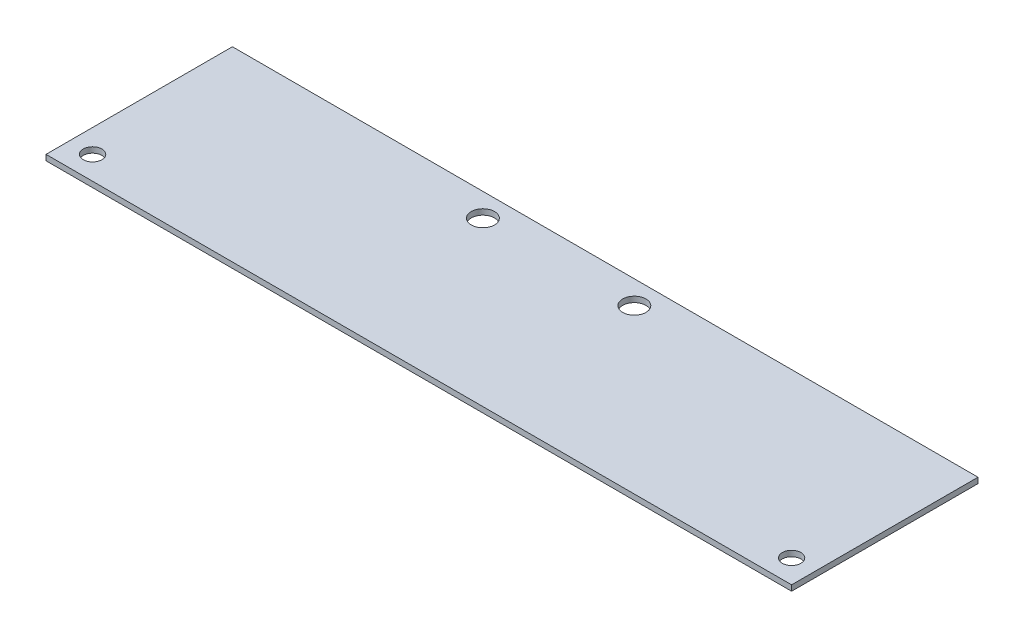
SolidWorks part; units mm, degrees
material "1023 Carbon Steel Sheet (SS)"
ref_plane "Front Plane" through (0, 0, 0) normal (0, 0, 1) x (1, 0, 0)
ref_plane "Top Plane" through (0, 0, 0) normal (0, 1, 0) x (1, 0, 0)
ref_plane "Right Plane" through (0, 0, 0) normal (1, 0, 0) x (0, 0, -1)
sketch "Sketch1" plane through (0, 0, 0) normal (0, 1, 0) x (1, 0, 0)
  line L1 (0, 0) -> (203.2, 0)
  line L2 (0, 0) -> (0, 50.8)
  line L3 (0, 50.8) -> (203.2, 50.8)
  line L4 (203.2, 0) -> (203.2, 50.8)
  circle A0 centre (6.35, 6.35) radius 2.54
  circle A1 centre (196.85, 6.35) radius 2.54
  circle A2 centre (74.6125, 44.45) radius 3.175
  circle A3 centre (115.8875, 44.45) radius 3.175
  dimension "D1" = 5.08
  dimension "D2" = 5.08
  dimension "D6" = 190.5
  dimension "D7" = 6.35
  dimension "D8" = 6.35
  dimension "D9" = 41.275
  dimension "D10" = 38.1
  dimension "D3" = 6.35
  dimension "D4" = 6.35
  dimension "D5" = 6.35
  dimension "D11" = 6.35
  dimension "D12" = 74.6125
extrude "Boss-Extrude1" add sketch "Sketch1" along normal blind 1.524
